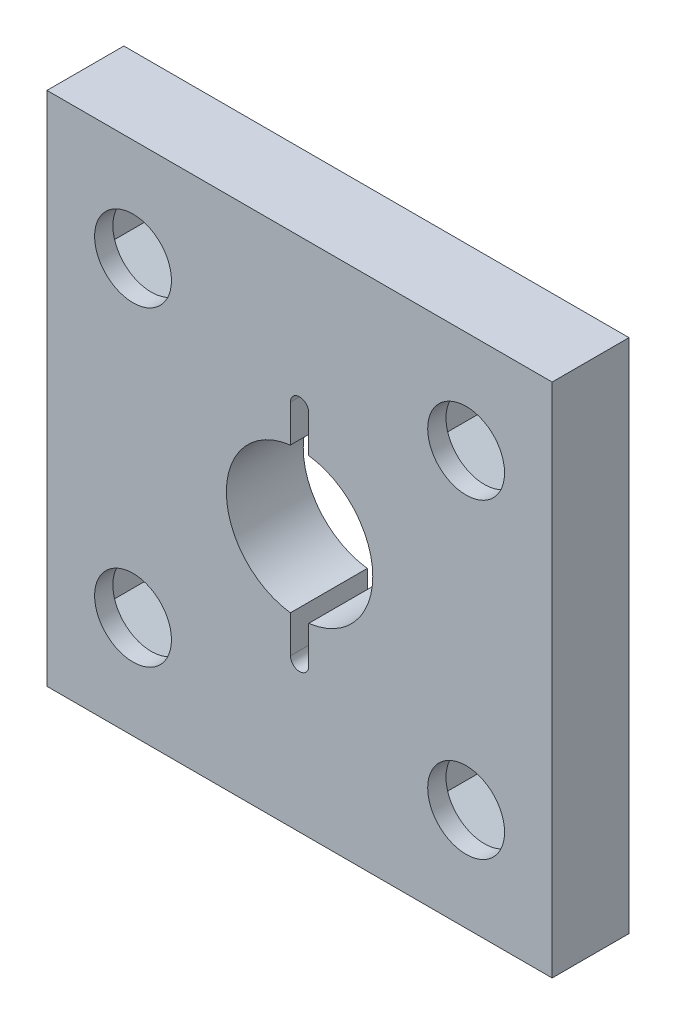
SolidWorks part; units mm, degrees
ref_plane "Front Plane" through (0, 0, 0) normal (0, 0, 1) x (1, 0, 0)
ref_plane "Top Plane" through (0, 0, 0) normal (0, 1, 0) x (1, 0, 0)
ref_plane "Right Plane" through (0, 0, 0) normal (1, 0, 0) x (0, 0, -1)
sketch "Sketch1" plane through (0, 0, 0) normal (0, 0, 1) x (1, 0, 0)
  line L0 (-8.89, 10.795) -> (8.89, 10.795) construction
  line L1 (17.526, 17.907) -> (-17.526, 17.907)
  line L2 (17.526, 17.907) -> (17.526, -17.907)
  line L3 (17.526, -17.907) -> (-17.526, -17.907)
  line L4 (-17.526, 17.907) -> (-17.526, -17.907)
  line L5 (17.526, 17.907) -> (-17.526, -17.907) construction
  line L6 (17.526, -17.907) -> (-17.526, 17.907) construction
  line L7 (0, 10.795) -> (0, -10.795) construction
  line L8 (-8.89, -10.795) -> (8.89, -10.795) construction
  circle A0 centre (-11.557, 10.795) radius 2.667
  circle A1 centre (11.557, 10.795) radius 2.667
  circle A2 centre (11.557, -10.795) radius 2.667
  circle A3 centre (-11.557, -10.795) radius 2.667
  point P0 (0, 0)
  point P22 (0, 0)
  dimension "D3" = 5.334
  dimension "D4" = 16.256
  dimension "D5" = 17.78
  dimension "D1" = 35.052
  dimension "D2" = 35.814
extrude "Boss-Extrude1" add sketch "Sketch1" along normal blind 5.334
sketch "Sketch2" plane through (0, 0, 0) normal (0, 0, -1) x (-1, 0, 0)
  line L1 (-11.557, 5.9557) -> (-7.366, 8.3753)
  line L2 (-7.366, 8.3753) -> (-7.366, 13.2147)
  line L3 (-7.366, 13.2147) -> (-11.557, 15.6343)
  line L4 (-11.557, 15.6343) -> (-15.748, 13.2147)
  line L5 (-15.748, 13.2147) -> (-15.748, 8.3753)
  line L6 (-15.748, 8.3753) -> (-11.557, 5.9557)
  line L7 (-11.557, -15.6343) -> (-7.366, -13.2147)
  line L8 (-7.366, -13.2147) -> (-7.366, -8.3753)
  line L9 (-7.366, -8.3753) -> (-11.557, -5.9557)
  line L10 (-11.557, -5.9557) -> (-15.748, -8.3753)
  line L11 (-15.748, -8.3753) -> (-15.748, -13.2147)
  line L12 (-15.748, -13.2147) -> (-11.557, -15.6343)
  line L13 (11.557, -15.6343) -> (15.748, -13.2147)
  line L14 (15.748, -13.2147) -> (15.748, -8.3753)
  line L15 (15.748, -8.3753) -> (11.557, -5.9557)
  line L16 (11.557, -5.9557) -> (7.366, -8.3753)
  line L17 (7.366, -8.3753) -> (7.366, -13.2147)
  line L18 (7.366, -13.2147) -> (11.557, -15.6343)
  line L19 (11.557, 5.9557) -> (15.748, 8.3753)
  line L20 (15.748, 8.3753) -> (15.748, 13.2147)
  line L21 (15.748, 13.2147) -> (11.557, 15.6343)
  line L22 (11.557, 15.6343) -> (7.366, 13.2147)
  line L23 (7.366, 13.2147) -> (7.366, 8.3753)
  line L24 (7.366, 8.3753) -> (11.557, 5.9557)
  circle A0 centre (-11.557, 10.795) radius 4.191 construction
  circle A1 centre (-11.557, -10.795) radius 4.191 construction
  circle A2 centre (11.557, -10.795) radius 4.191 construction
  circle A3 centre (11.557, 10.795) radius 4.191 construction
  point P28 (-7.366, 10.795)
  dimension "D1" = 8.382
extrude "Cut-Extrude1" cut sketch "Sketch2" against normal offset from surface (4.064 mm away) 1.27 up to face at (0, 0, 5.334)
sketch "Sketch3" plane through (0, 0, 5.334) normal (0, 0, 1) x (1, 0, 0)
  circle A0 centre (0, 0) radius 5.08
  dimension "D1" = 10.16
extrude "Cut-Extrude2" cut sketch "Sketch3" against normal through all
sketch "Sketch4" plane through (0, 0, 5.334) normal (0, 0, 1) x (1, 0, 0)
  line L0 (0, -7.62) -> (0, 7.62) construction
  line L1 (-0.635, -7.62) -> (-0.635, 7.62)
  line L2 (0.635, -7.62) -> (0.635, 7.62)
  arc A0 (-0.635, -7.62) -> (0.635, -7.62) centre (0, -7.62) ccw
  arc A1 (0.635, 7.62) -> (-0.635, 7.62) centre (0, 7.62) ccw
  point P2 (0, 0)
  dimension "D1" = 1.27
  dimension "D2" = 15.24
extrude "Cut-Extrude3" cut sketch "Sketch4" against normal through all
